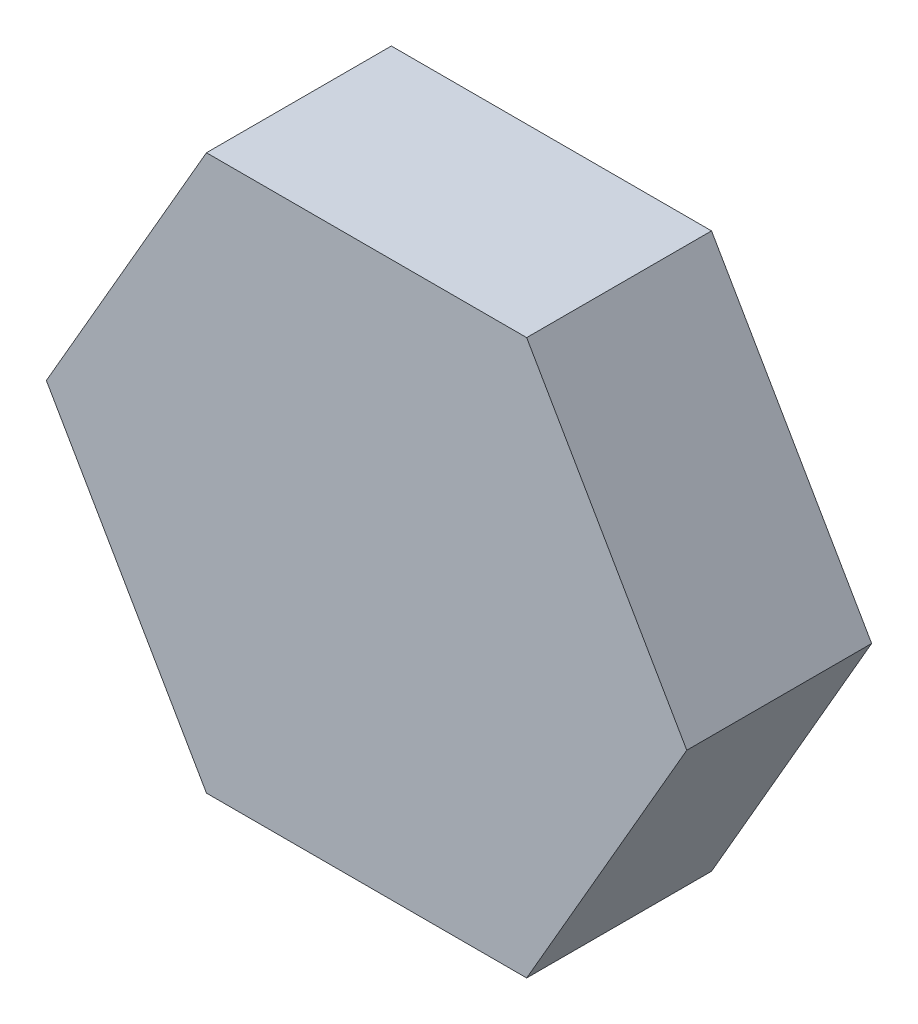
SolidWorks part; units mm, degrees
ref_plane "Front Plane" through (0, 0, 0) normal (0, 0, 1) x (1, 0, 0)
ref_plane "Top Plane" through (0, 0, 0) normal (0, 1, 0) x (1, 0, 0)
ref_plane "Right Plane" through (0, 0, 0) normal (1, 0, 0) x (0, 0, -1)
sketch "Sketch1" plane through (0, 0, 0) normal (0, 0, 1) x (1, 0, 0)
  line L1 (8.6603, 15) -> (-8.6603, 15)
  line L2 (-8.6603, 15) -> (-17.3205, 0)
  line L3 (-17.3205, 0) -> (-8.6603, -15)
  line L4 (-8.6603, -15) -> (8.6603, -15)
  line L5 (8.6603, -15) -> (17.3205, 0)
  line L6 (17.3205, 0) -> (8.6603, 15)
  circle A0 centre (0, 0) radius 15 construction
  dimension "D1" = 30
extrude "Boss-Extrude1" add sketch "Sketch1" along normal blind 10
